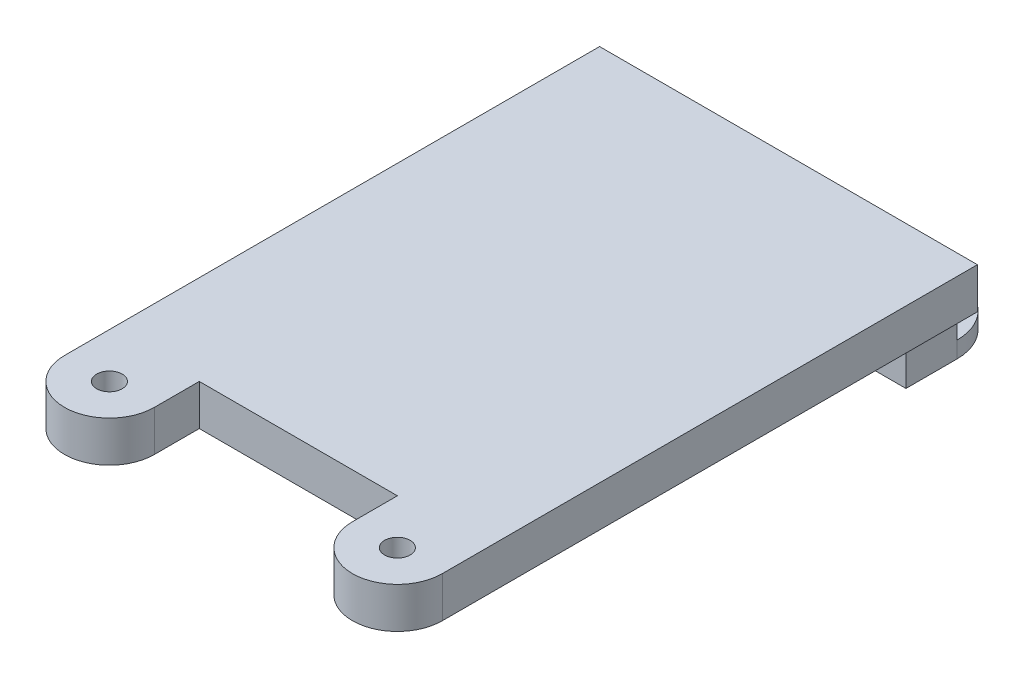
SolidWorks part; units mm, degrees
ref_plane "Front Plane" through (0, 0, 0) normal (0, 0, 1) x (1, 0, 0)
ref_plane "Top Plane" through (0, 0, 0) normal (0, 1, 0) x (1, 0, 0)
ref_plane "Right Plane" through (0, 0, 0) normal (1, 0, 0) x (0, 0, -1)
sketch "Sketch1" plane through (0, 0, 0) normal (0, 1, 0) x (1, 0, 0)
  line L0 (-9.25, -12) -> (-9.25, -14.2)
  line L1 (-9.25, -12) -> (9.25, -12)
  line L2 (-9.25, -12) -> (-9.25, 12)
  line L3 (-9.25, 12) -> (9.25, 12)
  line L4 (9.25, -12) -> (9.25, 12)
  line L5 (-9.25, -12) -> (9.25, 12) construction
  line L6 (-9.25, 12) -> (9.25, -12) construction
  line L7 (-4.85, -14.2) -> (-4.85, -12)
  line L8 (9.25, -12) -> (9.25, -14.2)
  line L9 (4.85, -14.2) -> (4.85, -12)
  arc A0 (-9.25, -14.2) -> (-4.85, -14.2) centre (-7.05, -14.2) ccw
  circle A1 centre (-7.05, -14.2) radius 0.625
  arc A2 (4.85, -14.2) -> (9.25, -14.2) centre (7.05, -14.2) ccw
  circle A3 centre (7.05, -14.2) radius 0.625
  point P0 (0, 0)
  dimension "D3" = 4.4
  dimension "D4" = 1.25
  dimension "D1" = 18.5
  dimension "D2" = 24
extrude "Boss-Extrude1" add sketch "Sketch1" along normal blind 2 contours L1 L4 L3 L2 | L0 A0 L7 L1 A1 | L9 A2 L8 L1 A3
sketch "Sketch2" plane through (0, 0, 0) normal (0, -1, 0) x (1, 0, 0)
  line L1 (-8.25, -12) -> (8.25, -12)
  line L2 (-8.25, -12) -> (-8.25, -9.5)
  line L3 (-8.25, -9.5) -> (8.25, -9.5)
  line L4 (8.25, -12) -> (8.25, -9.5)
  line L5 (-9.25, -12) -> (9.25, -12) construction
  line L6 (-9.25, 14.2) -> (-9.25, -12) construction
  line L7 (9.25, 14.2) -> (9.25, -12) construction
  dimension "D1" = 2.5
  dimension "D2" = 1
  dimension "D3" = 1
extrude "Boss-Extrude2" add sketch "Sketch2" along normal blind 2.5
sketch "Sketch3" plane through (0, -2.5, 0) normal (0, -1, 0) x (-1, 0, 0)
  line L0 (8.25, 9.5) -> (8.25, 12) construction
  line L1 (-8.25, 12) -> (8.25, 12)
  line L2 (-8.25, 12) -> (-8.25, 14.5)
  line L3 (-8.25, 14.5) -> (8.25, 14.5)
  line L4 (8.25, 12) -> (8.25, 14.5)
  dimension "D1" = 2.5
extrude "Boss-Extrude3" add sketch "Sketch3" against normal blind 0.8
fillet "Fillet2" radius 2.5 2 edges at (-8.25, -2.1, -14.5) (8.25, -2.1, -14.5)
